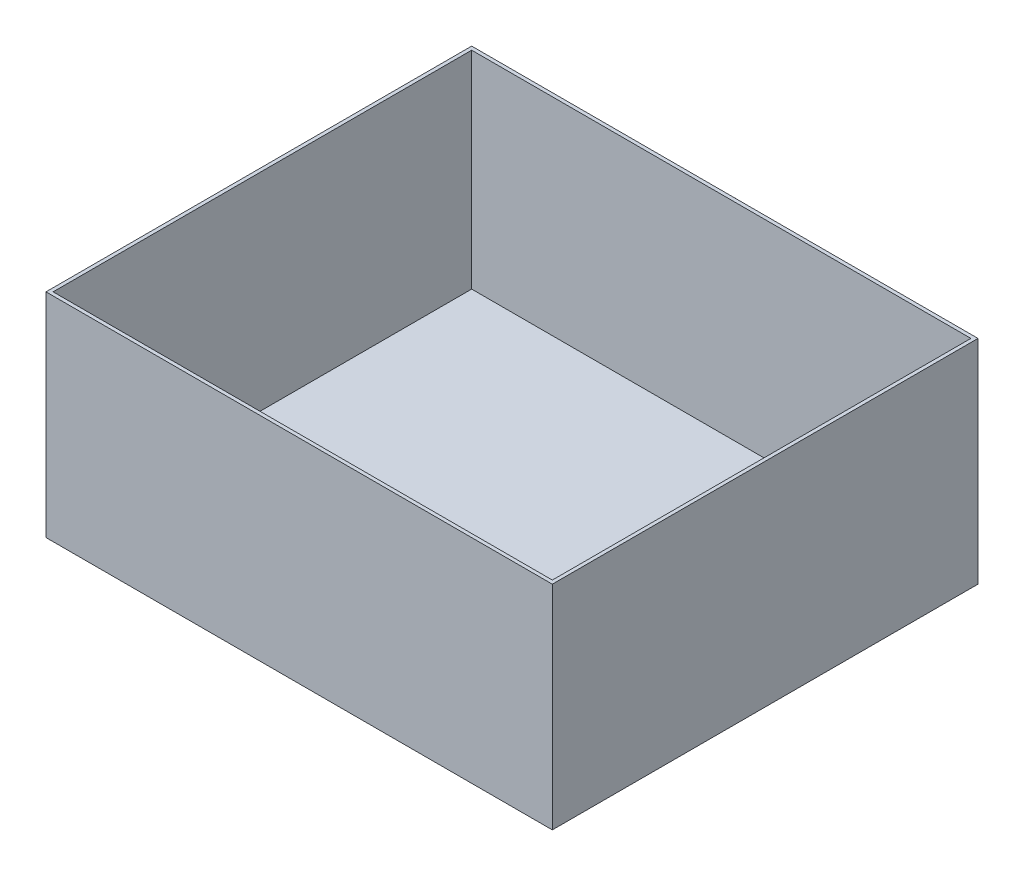
SolidWorks part; units mm, degrees
ref_plane "Front Plane" through (0, 0, 0) normal (0, 0, 1) x (1, 0, 0)
ref_plane "Top Plane" through (0, 0, 0) normal (0, 1, 0) x (1, 0, 0)
ref_plane "Right Plane" through (0, 0, 0) normal (1, 0, 0) x (0, 0, -1)
sketch "Sketch1" plane through (0, 0, 0) normal (0, 1, 0) x (1, 0, 0)
  line L1 (0, 0) -> (214.1055, 0)
  line L2 (0, 0) -> (0, 180)
  line L3 (0, 180) -> (214.1055, 180)
  line L4 (214.1055, 0) -> (214.1055, 180)
extrude "Boss-Extrude1" add sketch "Sketch1" along normal blind 90
sketch "Sketch2" plane through (0, 90, 0) normal (0, 1, 0) x (1, 0, 0)
  line L0 (0, 0) -> (214.1055, 180) construction
  line L1 (107.0528, 1.5) -> (107.0528, 178.5) construction
  line L3 (1.5, 178.5) -> (212.6055, 178.5)
  line L4 (1.5, 178.5) -> (1.5, 1.5)
  line L5 (1.5, 1.5) -> (212.6055, 1.5)
  line L6 (212.6055, 178.5) -> (212.6055, 1.5)
  line L8 (214.1055, 0) -> (212.6055, 0) construction
  line L9 (214.1055, 0) -> (214.1055, 1.5) construction
  line L10 (214.1055, 1.5) -> (212.6055, 1.5) construction
  line L11 (212.6055, 0) -> (212.6055, 1.5) construction
  line L12 (0, 180) -> (1.5, 180) construction
  line L13 (0, 180) -> (0, 232.8952) construction
  line L14 (0, 232.8952) -> (1.5, 232.8952) construction
  line L15 (1.5, 180) -> (1.5, 232.8952) construction
  point P6 (107.0528, 90)
extrude "Cut-Extrude1" cut sketch "Sketch2" against normal blind 87.5
